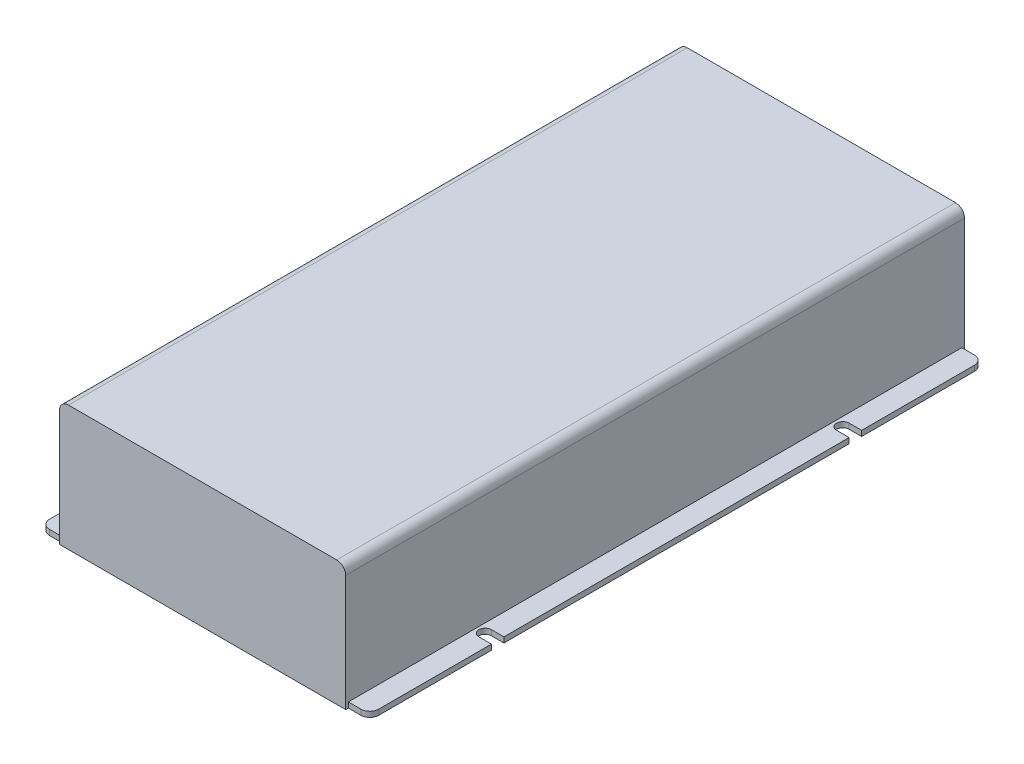
SolidWorks part; units mm, degrees
ref_plane "Alzado" through (0, 0, 0) normal (0, 0, 1) x (1, 0, 0)
ref_plane "Planta" through (0, 0, 0) normal (0, 1, 0) x (1, 0, 0)
ref_plane "Vista lateral" through (0, 0, 0) normal (1, 0, 0) x (0, 0, -1)
sketch "Croquis1" plane through (0, 0, 0) normal (0, 0, 1) x (1, 0, 0)
  line L0 (0, 0) -> (80631.0132, 0) construction
  line L2 (-80, 0) -> (80, 0)
  line L3 (-80, 0) -> (-80, 70)
  line L4 (-80, 70) -> (80, 70)
  line L5 (80, 0) -> (80, 70)
  point P7 (0, 70)
  dimension "D1" = 160
  dimension "D2" = 70
extrude "Saliente-Extruir1" add sketch "Croquis1" along normal mid plane 346
sketch "Croquis2" plane through (0, 0, 0) normal (0, -1, 0) x (1, 0, 0)
  line L0 (-80, 173) -> (80, 173) construction
  line L1 (80, 171.5) -> (92, 171.5)
  line L2 (80, 171.5) -> (80, -171.5)
  line L3 (80, -171.5) -> (92, -171.5)
  line L4 (92, 171.5) -> (92, -171.5)
  line L5 (-80, -173) -> (80, -173) construction
  dimension "D1" = 12
  dimension "D2" = 1.5
  dimension "D3" = 1.5
extrude "Saliente-Extruir2" add sketch "Croquis2" against normal blind 3
sketch "Croquis3" plane through (0, 3, 0) normal (0, 1, 0) x (1, 0, 0)
  line L0 (85, -103.5) -> (92, -103.5)
  line L3 (92, 171.5) -> (92, -171.5) construction
  line L4 (85, -96.5) -> (92, -96.5)
  line L5 (92, -96.5) -> (92, -103.5)
  line L6 (80, -173) -> (80, -171.5) construction
  line L7 (-80, -173) -> (80, -173) construction
  arc A2 (85, -103.5) -> (85, -96.5) centre (85, -100) cw
  dimension "D1" = 3.5
  dimension "D2" = 5
  dimension "D3" = 73
extrude "Cortar-Extruir1" cut sketch "Croquis3" against normal through all
mirror "Simetría1" about plane through (0, 0, 0) normal (0, 0, 1) of "Cortar-Extruir1"
mirror "Simetría5" about plane through (0, 0, 0) normal (1, 0, 0) of bodies 104
fillet "Redondeo1" radius 5 6 edges at (-92, 1.5, 171.5) (-92, 1.5, -171.5) (92, 1.5, 171.5) (92, 1.5, -171.5) (80, 70, 0) (-80, 70, 0)
